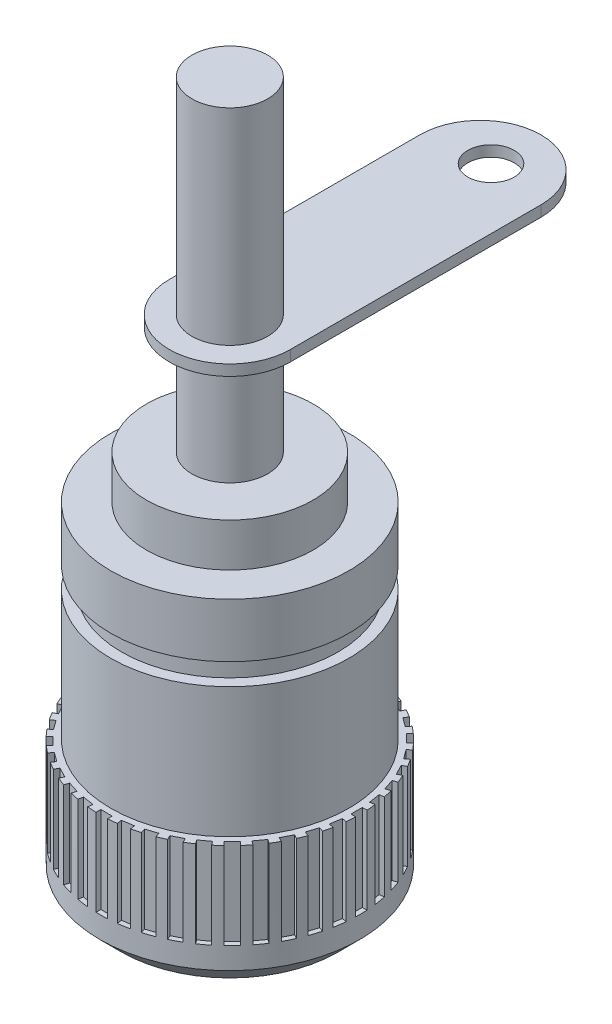
SolidWorks part; units mm, degrees
ref_plane "Front Plane" through (0, 0, 0) normal (0, 0, 1) x (1, 0, 0)
ref_plane "Top Plane" through (0, 0, 0) normal (0, 1, 0) x (1, 0, 0)
ref_plane "Right Plane" through (0, 0, 0) normal (1, 0, 0) x (0, 0, -1)
sketch "Sketch1" plane through (0, 0, 0) normal (0, 1, 0) x (1, 0, 0)
  circle A0 centre (0, 0) radius 6
  dimension "D1" = 12
extrude "Boss-Extrude1" add sketch "Sketch1" along normal blind 12
sketch "Sketch2" plane through (0, 12, 0) normal (0, 1, 0) x (1, 0, 0)
  circle A0 centre (0, 0) radius 5.5
  circle A1 centre (0, 0) radius 8.1182
  dimension "D1" = 11
extrude "Cut-Extrude1" cut sketch "Sketch2" against normal blind 6
chamfer "Chamfer1" distance 1 angle 45 1 edges at (0, 0, 6)
sketch "Sketch3" plane through (0, 0, 0) normal (0, -1, 0) x (1, 0, 0)
  circle A0 centre (0, 0) radius 3.25
  dimension "D1" = 6.5
extrude "Cut-Extrude2" cut sketch "Sketch3" against normal blind 6
sketch "Sketch5" plane through (0, 12, 0) normal (0, 1, 0) x (1, 0, 0)
  circle A0 centre (0, 0) radius 5
  dimension "D1" = 10
extrude "Boss-Extrude2" add sketch "Sketch5" along normal blind 1
sketch "Sketch6" plane through (0, 13, 0) normal (0, 1, 0) x (1, 0, 0)
  circle A0 centre (0, 0) radius 5.5
extrude "Boss-Extrude3" add sketch "Sketch6" along normal blind 2.5
sketch "Sketch7" plane through (0, 6, 0) normal (0, -1, 0) x (1, 0, 0)
  circle A0 centre (0, 0) radius 2.7165
  circle A1 centre (0, 0) radius 2.4857
extrude "Boss-Extrude4" add sketch "Sketch7" along normal blind 4.5
sketch "Sketch8" plane through (0, 15.5, 0) normal (0, 1, 0) x (1, 0, 0)
  circle A0 centre (0, 0) radius 3.85
  dimension "D1" = 7.7
extrude "Boss-Extrude5" add sketch "Sketch8" along normal blind 2
sketch "Sketch9" plane through (0, 17.5, 0) normal (0, 1, 0) x (1, 0, 0)
  circle A0 centre (0, 0) radius 1.75
  dimension "D1" = 3.5
extrude "Boss-Extrude6" add sketch "Sketch9" along normal blind 15
sketch "Sketch10" plane through (0, 17.5, 0) normal (0, 1, 0) x (1, 0, 0)
  line L0 (0, 0) -> (0, 11.572) construction
  line L1 (-2.7978, 0) -> (-2.7978, 11.572)
  line L2 (2.7978, 0) -> (2.7978, 11.572)
  arc A0 (-2.7978, 0) -> (2.7978, 0) centre (0, 0) ccw
  arc A1 (2.7978, 11.572) -> (-2.7978, 11.572) centre (0, 11.572) ccw
  point P3 (0, 5.786)
extrude "Boss-Extrude7" add sketch "Sketch10" along normal blind 0.5 from offset 5
sketch "Sketch11" plane through (0, 22.5, 0) normal (0, -1, 0) x (1, 0, 0)
  circle A0 centre (0, -12.0618) radius 1.0712
extrude "Cut-Extrude3" cut sketch "Sketch11" against normal blind 0.5
sketch "Sketch12" plane through (0, 0, 0) normal (0, -1, 0) x (1, 0, 0)
  line L0 (0.8247, 6.3742) -> (0.723, 5.7316)
  line L1 (-0.1826, 6.4247) -> (0.3452, 6.4247)
  line L2 (-0.1826, 6.4247) -> (-0.1826, 5.7742)
  line L3 (-0.1826, 5.7742) -> (0.3452, 5.7742)
  line L4 (0.3452, 6.4247) -> (0.3452, 5.7742)
  line L5 (0.8247, 6.3742) -> (1.346, 6.2916)
  line L6 (1.346, 6.2916) -> (1.2443, 5.6491)
  line L7 (0.723, 5.7316) -> (1.2443, 5.6491)
  line L8 (1.8117, 6.1667) -> (1.6107, 5.548)
  line L9 (1.8117, 6.1667) -> (2.3137, 6.0036)
  line L10 (2.3137, 6.0036) -> (2.1127, 5.3849)
  line L11 (1.6107, 5.548) -> (2.1127, 5.3849)
  line L12 (2.7541, 5.8074) -> (2.4587, 5.2277)
  line L13 (2.7541, 5.8074) -> (3.2244, 5.5677)
  line L14 (3.2244, 5.5677) -> (2.929, 4.9881)
  line L15 (2.4587, 5.2277) -> (2.929, 4.9881)
  line L16 (3.6287, 5.305) -> (3.2463, 4.7787)
  line L17 (3.6287, 5.305) -> (4.0557, 4.9948)
  line L18 (4.0557, 4.9948) -> (3.6733, 4.4685)
  line L19 (3.2463, 4.7787) -> (3.6733, 4.4685)
  line L20 (4.4139, 4.6721) -> (3.9539, 4.2121)
  line L21 (4.4139, 4.6721) -> (4.7871, 4.2989)
  line L22 (4.7871, 4.2989) -> (4.3271, 3.8388)
  line L23 (3.9539, 4.2121) -> (4.3271, 3.8388)
  line L24 (5.0904, 3.9241) -> (4.5641, 3.5417)
  line L25 (5.0904, 3.9241) -> (5.4006, 3.4971)
  line L26 (5.4006, 3.4971) -> (4.8743, 3.1147)
  line L27 (4.5641, 3.5417) -> (4.8743, 3.1147)
  line L28 (5.6416, 3.0794) -> (5.0619, 2.7841)
  line L29 (5.6416, 3.0794) -> (5.8812, 2.6092)
  line L30 (5.8812, 2.6092) -> (5.3016, 2.3138)
  line L31 (5.0619, 2.7841) -> (5.3016, 2.3138)
  line L32 (6.0539, 2.159) -> (5.4351, 1.958)
  line L33 (6.0539, 2.159) -> (6.217, 1.657)
  line L34 (6.217, 1.657) -> (5.5983, 1.456)
  line L35 (5.4351, 1.958) -> (5.5983, 1.456)
  line L36 (6.3171, 1.1854) -> (5.6745, 1.0836)
  line L37 (6.3171, 1.1854) -> (6.3996, 0.6641)
  line L38 (6.3996, 0.6641) -> (5.7571, 0.5623)
  line L39 (5.6745, 1.0836) -> (5.7571, 0.5623)
  line L40 (6.4247, 0.1826) -> (5.7742, 0.1826)
  line L41 (6.4247, 0.1826) -> (6.4247, -0.3452)
  line L42 (6.4247, -0.3452) -> (5.7742, -0.3452)
  line L43 (5.7742, 0.1826) -> (5.7742, -0.3452)
  line L44 (6.3742, -0.8247) -> (5.7316, -0.723)
  line L45 (6.3742, -0.8247) -> (6.2916, -1.346)
  line L46 (6.2916, -1.346) -> (5.6491, -1.2443)
  line L47 (5.7316, -0.723) -> (5.6491, -1.2443)
  line L48 (6.1667, -1.8117) -> (5.548, -1.6107)
  line L49 (6.1667, -1.8117) -> (6.0036, -2.3137)
  line L50 (6.0036, -2.3137) -> (5.3849, -2.1127)
  line L51 (5.548, -1.6107) -> (5.3849, -2.1127)
  line L52 (5.8074, -2.7541) -> (5.2277, -2.4587)
  line L53 (5.8074, -2.7541) -> (5.5677, -3.2244)
  line L54 (5.5677, -3.2244) -> (4.9881, -2.929)
  line L55 (5.2277, -2.4587) -> (4.9881, -2.929)
  line L56 (5.305, -3.6287) -> (4.7787, -3.2463)
  line L57 (5.305, -3.6287) -> (4.9948, -4.0557)
  line L58 (4.9948, -4.0557) -> (4.4685, -3.6733)
  line L59 (4.7787, -3.2463) -> (4.4685, -3.6733)
  line L60 (4.6721, -4.4139) -> (4.2121, -3.9539)
  line L61 (4.6721, -4.4139) -> (4.2989, -4.7871)
  line L62 (4.2989, -4.7871) -> (3.8388, -4.3271)
  line L63 (4.2121, -3.9539) -> (3.8388, -4.3271)
  line L64 (3.9241, -5.0904) -> (3.5417, -4.5641)
  line L65 (3.9241, -5.0904) -> (3.4971, -5.4006)
  line L66 (3.4971, -5.4006) -> (3.1147, -4.8743)
  line L67 (3.5417, -4.5641) -> (3.1147, -4.8743)
  line L68 (3.0794, -5.6416) -> (2.7841, -5.0619)
  line L69 (3.0794, -5.6416) -> (2.6092, -5.8812)
  line L70 (2.6092, -5.8812) -> (2.3138, -5.3016)
  line L71 (2.7841, -5.0619) -> (2.3138, -5.3016)
  line L72 (2.159, -6.0539) -> (1.958, -5.4351)
  line L73 (2.159, -6.0539) -> (1.657, -6.217)
  line L74 (1.657, -6.217) -> (1.456, -5.5983)
  line L75 (1.958, -5.4351) -> (1.456, -5.5983)
  line L76 (1.1854, -6.3171) -> (1.0836, -5.6745)
  line L77 (1.1854, -6.3171) -> (0.6641, -6.3996)
  line L78 (0.6641, -6.3996) -> (0.5623, -5.7571)
  line L79 (1.0836, -5.6745) -> (0.5623, -5.7571)
  line L80 (0.1826, -6.4247) -> (0.1826, -5.7742)
  line L81 (0.1826, -6.4247) -> (-0.3452, -6.4247)
  line L82 (-0.3452, -6.4247) -> (-0.3452, -5.7742)
  line L83 (0.1826, -5.7742) -> (-0.3452, -5.7742)
  line L84 (-0.8247, -6.3742) -> (-0.723, -5.7316)
  line L85 (-0.8247, -6.3742) -> (-1.346, -6.2916)
  line L86 (-1.346, -6.2916) -> (-1.2443, -5.6491)
  line L87 (-0.723, -5.7316) -> (-1.2443, -5.6491)
  line L88 (-1.8117, -6.1667) -> (-1.6107, -5.548)
  line L89 (-1.8117, -6.1667) -> (-2.3137, -6.0036)
  line L90 (-2.3137, -6.0036) -> (-2.1127, -5.3849)
  line L91 (-1.6107, -5.548) -> (-2.1127, -5.3849)
  line L92 (-2.7541, -5.8074) -> (-2.4587, -5.2277)
  line L93 (-2.7541, -5.8074) -> (-3.2244, -5.5677)
  line L94 (-3.2244, -5.5677) -> (-2.929, -4.9881)
  line L95 (-2.4587, -5.2277) -> (-2.929, -4.9881)
  line L96 (-3.6287, -5.305) -> (-3.2463, -4.7787)
  line L97 (-3.6287, -5.305) -> (-4.0557, -4.9948)
  line L98 (-4.0557, -4.9948) -> (-3.6733, -4.4685)
  line L99 (-3.2463, -4.7787) -> (-3.6733, -4.4685)
  line L100 (-4.4139, -4.6721) -> (-3.9539, -4.2121)
  line L101 (-4.4139, -4.6721) -> (-4.7871, -4.2989)
  line L102 (-4.7871, -4.2989) -> (-4.3271, -3.8388)
  line L103 (-3.9539, -4.2121) -> (-4.3271, -3.8388)
  line L104 (-5.0904, -3.9241) -> (-4.5641, -3.5417)
  line L105 (-5.0904, -3.9241) -> (-5.4006, -3.4971)
  line L106 (-5.4006, -3.4971) -> (-4.8743, -3.1147)
  line L107 (-4.5641, -3.5417) -> (-4.8743, -3.1147)
  line L108 (-5.6416, -3.0794) -> (-5.0619, -2.7841)
  line L109 (-5.6416, -3.0794) -> (-5.8812, -2.6092)
  line L110 (-5.8812, -2.6092) -> (-5.3016, -2.3138)
  line L111 (-5.0619, -2.7841) -> (-5.3016, -2.3138)
  line L112 (-6.0539, -2.159) -> (-5.4351, -1.958)
  line L113 (-6.0539, -2.159) -> (-6.217, -1.657)
  line L114 (-6.217, -1.657) -> (-5.5983, -1.456)
  line L115 (-5.4351, -1.958) -> (-5.5983, -1.456)
  line L116 (-6.3171, -1.1854) -> (-5.6745, -1.0836)
  line L117 (-6.3171, -1.1854) -> (-6.3996, -0.6641)
  line L118 (-6.3996, -0.6641) -> (-5.7571, -0.5623)
  line L119 (-5.6745, -1.0836) -> (-5.7571, -0.5623)
  line L120 (-6.4247, -0.1826) -> (-5.7742, -0.1826)
  line L121 (-6.4247, -0.1826) -> (-6.4247, 0.3452)
  line L122 (-6.4247, 0.3452) -> (-5.7742, 0.3452)
  line L123 (-5.7742, -0.1826) -> (-5.7742, 0.3452)
  line L124 (-6.3742, 0.8247) -> (-5.7316, 0.723)
  line L125 (-6.3742, 0.8247) -> (-6.2916, 1.346)
  line L126 (-6.2916, 1.346) -> (-5.6491, 1.2443)
  line L127 (-5.7316, 0.723) -> (-5.6491, 1.2443)
  line L128 (-6.1667, 1.8117) -> (-5.548, 1.6107)
  line L129 (-6.1667, 1.8117) -> (-6.0036, 2.3137)
  line L130 (-6.0036, 2.3137) -> (-5.3849, 2.1127)
  line L131 (-5.548, 1.6107) -> (-5.3849, 2.1127)
  line L132 (-5.8074, 2.7541) -> (-5.2277, 2.4587)
  line L133 (-5.8074, 2.7541) -> (-5.5677, 3.2244)
  line L134 (-5.5677, 3.2244) -> (-4.9881, 2.929)
  line L135 (-5.2277, 2.4587) -> (-4.9881, 2.929)
  line L136 (-5.305, 3.6287) -> (-4.7787, 3.2463)
  line L137 (-5.305, 3.6287) -> (-4.9948, 4.0557)
  line L138 (-4.9948, 4.0557) -> (-4.4685, 3.6733)
  line L139 (-4.7787, 3.2463) -> (-4.4685, 3.6733)
  line L140 (-4.6721, 4.4139) -> (-4.2121, 3.9539)
  line L141 (-4.6721, 4.4139) -> (-4.2989, 4.7871)
  line L142 (-4.2989, 4.7871) -> (-3.8388, 4.3271)
  line L143 (-4.2121, 3.9539) -> (-3.8388, 4.3271)
  line L144 (-3.9241, 5.0904) -> (-3.5417, 4.5641)
  line L145 (-3.9241, 5.0904) -> (-3.4971, 5.4006)
  line L146 (-3.4971, 5.4006) -> (-3.1147, 4.8743)
  line L147 (-3.5417, 4.5641) -> (-3.1147, 4.8743)
  line L148 (-3.0794, 5.6416) -> (-2.7841, 5.0619)
  line L149 (-3.0794, 5.6416) -> (-2.6092, 5.8812)
  line L150 (-2.6092, 5.8812) -> (-2.3138, 5.3016)
  line L151 (-2.7841, 5.0619) -> (-2.3138, 5.3016)
  line L152 (-2.159, 6.0539) -> (-1.958, 5.4351)
  line L153 (-2.159, 6.0539) -> (-1.657, 6.217)
  line L154 (-1.657, 6.217) -> (-1.456, 5.5983)
  line L155 (-1.958, 5.4351) -> (-1.456, 5.5983)
  line L156 (-1.1854, 6.3171) -> (-1.0836, 5.6745)
  line L157 (-1.1854, 6.3171) -> (-0.6641, 6.3996)
  line L158 (-0.6641, 6.3996) -> (-0.5623, 5.7571)
  line L159 (-1.0836, 5.6745) -> (-0.5623, 5.7571)
  point P162 (0, 0)
  dimension "D1" = 40
extrude "Cut-Extrude4" cut sketch "Sketch12" against normal blind 8.5 from offset 2
